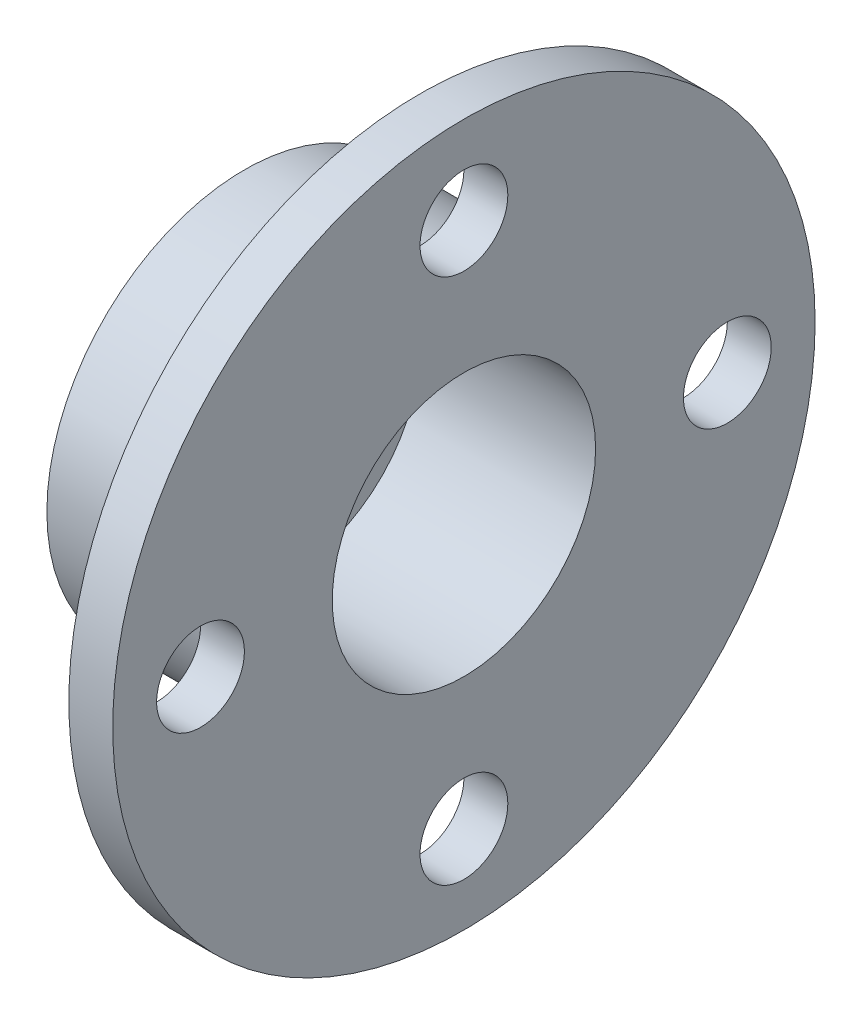
SolidWorks part; units mm, degrees
ref_plane "Front Plane" through (0, 0, 0) normal (0, 0, 1) x (1, 0, 0)
ref_plane "Top Plane" through (0, 0, 0) normal (0, 1, 0) x (1, 0, 0)
ref_plane "Right Plane" through (0, 0, 0) normal (1, 0, 0) x (0, 0, -1)
sketch "Sketch1" plane through (0, 0, 0) normal (0, 0, 1) x (1, 0, 0)
  line L0 (0, 0) -> (-484.2028, 0) construction
  line L1 (-151.1276, 114.3) -> (-49.5276, 114.3)
  line L2 (-24.1276, 203.2) -> (-49.5276, 203.2)
  line L5 (-49.5276, 203.2) -> (-49.5276, 114.3)
  line L6 (-24.1276, 76.2) -> (-125.7276, 76.2)
  line L11 (-151.1276, 114.3) -> (-151.1276, 50.8)
  line L12 (-151.1276, 50.8) -> (-125.7276, 50.8)
  line L13 (-125.7276, 76.2) -> (-125.7276, 50.8)
  line L14 (-24.1276, 203.2) -> (-24.1276, 76.2)
  dimension "D1" = 76.2
  dimension "D2" = 203.2
  dimension "D3" = 25.4
  dimension "D4" = 114.3
  dimension "D5" = 25.4
  dimension "D6" = 127
  dimension "D7" = 50.8
revolve "Revolve1" add sketch "Sketch1" angle 360 about L0
sketch "Sketch2" plane through (-24.1276, 0, 0) normal (1, 0, 0) x (0, 0, -1)
  line L0 (0, 152.4) -> (0, -152.4) construction
  line L1 (-152.4, 0) -> (152.4, 0) construction
  circle A0 centre (0, 0) radius 152.4
  circle A1 centre (0, 152.4) radius 25.4
  circle A2 centre (-152.4, 0) radius 25.4
  circle A3 centre (152.4, 0) radius 25.4
  circle A4 centre (0, -152.4) radius 25.4
  dimension "D1" = 304.8
  dimension "D2" = 50.8
  dimension "D3" = 50.8
extrude "Cut-Extrude1" cut sketch "Sketch2" against normal through all contours A0 A1 | A0 A1 | A0 A3 | A0 A3 | A0 A4 | A0 A4 | A0 A2 | A0 A2
